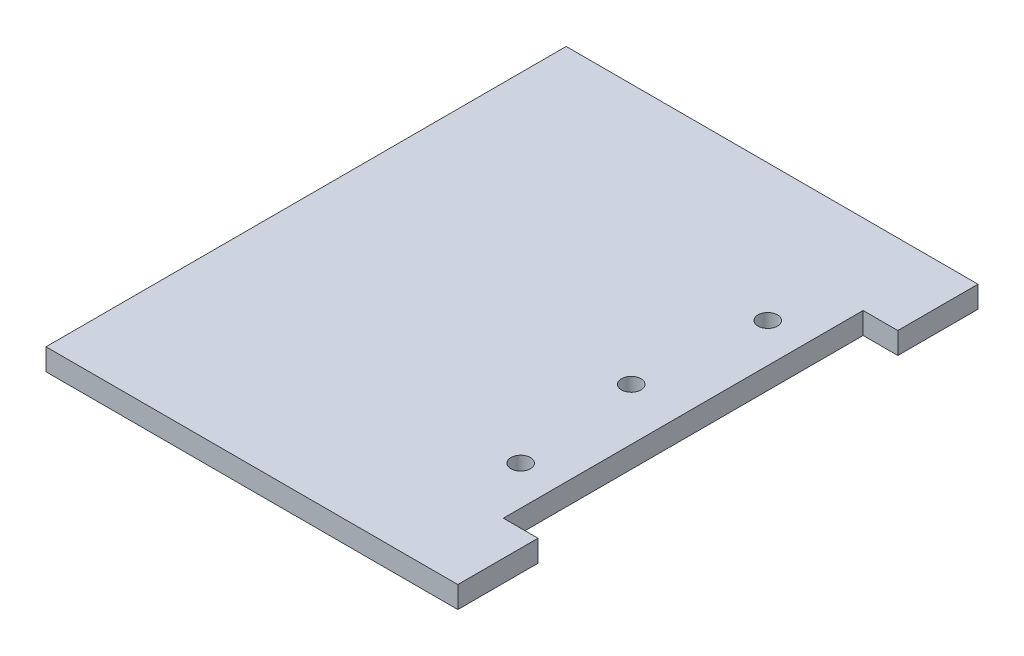
SolidWorks part; units mm, degrees
ref_plane "Front" through (0, 0, 0) normal (0, 0, 1) x (1, 0, 0)
ref_plane "Top" through (0, 0, 0) normal (0, 1, 0) x (1, 0, 0)
ref_plane "Right" through (0, 0, 0) normal (1, 0, 0) x (0, 0, -1)
sketch "Sketch1" plane through (0, 0, 0) normal (0, 1, 0) x (1, 0, 0)
  line L1 (-47.5, -60) -> (47.5, -60)
  line L2 (-47.5, -60) -> (-47.5, 60)
  line L3 (-47.5, 60) -> (47.5, 60)
  line L4 (47.5, -60) -> (47.5, 60)
  line L5 (-47.5, -60) -> (47.5, 60) construction
  line L6 (-47.5, 60) -> (47.5, -60) construction
  point P0 (0, 0)
  dimension "D1" = 95
  dimension "D2" = 120
extrude "Boss-Extrude1" add sketch "Sketch1" along normal blind 5
sketch "Sketch2" plane through (47.5, 0, 0) normal (1, 0, 0) x (0, 0, -1)
  line L0 (-60, 5) -> (60, 5) construction
  line L1 (-41.5, 5) -> (41.5, 5)
  line L2 (-41.5, 5) -> (-41.5, 0)
  line L3 (-41.5, 0) -> (41.5, 0)
  line L4 (41.5, 5) -> (41.5, 0)
  line L5 (-60, 0) -> (60, 0) construction
  dimension "D1" = 83
  dimension "D2" = 41.5
extrude "Cut-Extrude1" cut sketch "Sketch2" against normal blind 8
hole_wizard "Ø4.5 (4.5) Diameter Hole1" positions "Sketch4" profile "Sketch3" hole size "Ø4.5" standard "ANSI Metric" end condition through all
sketch "Sketch4" plane through (0, 5, 0) normal (0, 1, 0) x (1, 0, 0)
  line L0 (30.5, -28.5) -> (30.5, 49971.5) construction
  line L1 (39.5, 41.5) -> (39.5, -41.5) construction
  point P0 (30.5, 28.5)
  point P2 (27.5, 0)
  point P4 (30.5, -28.5)
  dimension "D1" = 57
  dimension "D2" = 28.5
  dimension "D3" = 3
  dimension "D4" = 12
sketch "Sketch3" plane through (30.5, 5, -28.5) normal (1, 0, 0) x (0, 0, 1)
  line L0 (0, 0) -> (0, 5)
  line L1 (0, 5) -> (2.25, 5)
  line L2 (2.25, 5) -> (2.25, 0)
  line L5 (2.25, 0) -> (0, 0)
  line L11 (0, -6.35) -> (0, 107.95) construction
  dimension "Thru Hole Dia." = 4.5
  dimension "Thru Hole Depth" = 5
